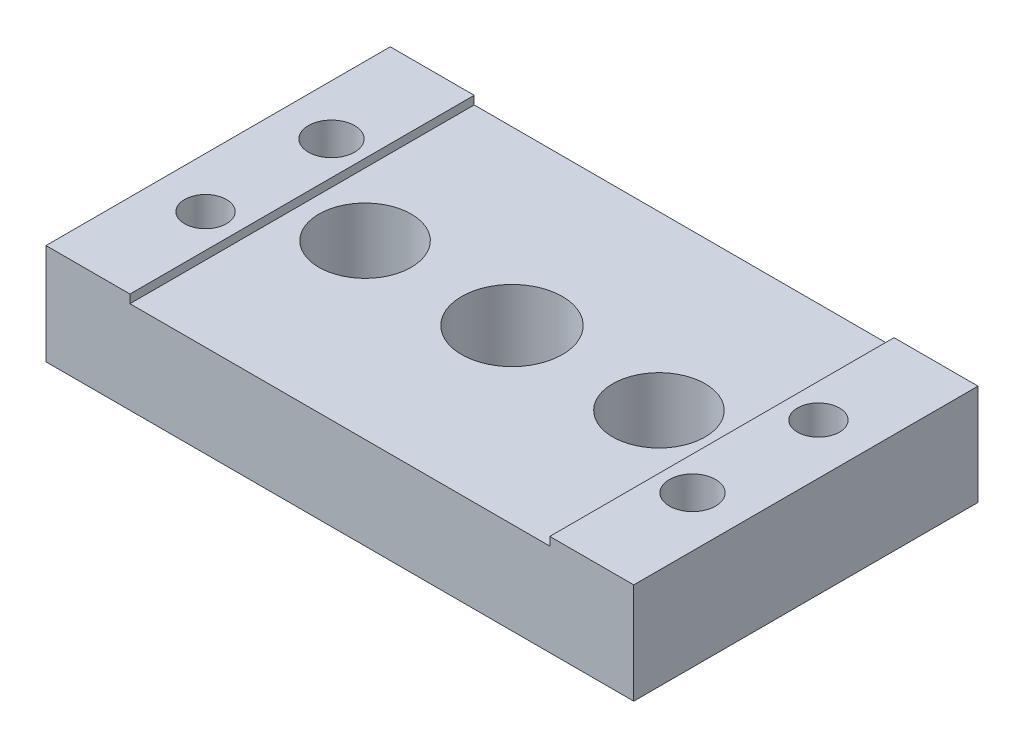
SolidWorks part; units mm, degrees
ref_plane "Front Plane" through (0, 0, 0) normal (0, 0, 1) x (1, 0, 0)
ref_plane "Top Plane" through (0, 0, 0) normal (0, 1, 0) x (1, 0, 0)
ref_plane "Right Plane" through (0, 0, 0) normal (1, 0, 0) x (0, 0, -1)
sketch "Sketch1" plane through (0, 0, 0) normal (0, 1, 0) x (1, 0, 0)
  line L1 (-35, 20.5) -> (35, 20.5)
  line L2 (-35, 20.5) -> (-35, -20.5)
  line L3 (-35, -20.5) -> (35, -20.5)
  line L4 (35, 20.5) -> (35, -20.5)
  line L5 (-35, 20.5) -> (35, -20.5) construction
  line L6 (-35, -20.5) -> (35, 20.5) construction
  point P0 (0, 0)
  dimension "D1" = 70
  dimension "D2" = 41
extrude "Boss-Extrude1" add sketch "Sketch1" along normal blind 12
sketch "Sketch2" plane through (0, 0, 20.5) normal (0, 0, 1) x (1, 0, 0)
  line L0 (-35, 12) -> (35, 12) construction
  line L1 (-25, 12) -> (25, 12)
  line L2 (-25, 12) -> (-25, 11)
  line L3 (-25, 11) -> (25, 11)
  line L4 (25, 12) -> (25, 11)
  line L5 (35, 12) -> (35, 0) construction
  line L6 (-35, 12) -> (-35, 0) construction
  dimension "D1" = 1
  dimension "D2" = 10
  dimension "D3" = 10
extrude "Cut-Extrude1" cut sketch "Sketch2" against normal blind 88
sketch "Sketch3" plane through (0, 0, 0) normal (0, -1, 0) x (1, 0, 0)
  line L0 (35, 20.5) -> (35, -20.5) construction
  line L1 (-35, -20.5) -> (-35, 20.5) construction
  line L2 (-35, 20.5) -> (35, 20.5) construction
  line L3 (35, -20.5) -> (-35, -20.5) construction
  circle A0 centre (29, -7.5) radius 2.5
  circle A1 centre (-29, 7.5) radius 2.5
  circle A2 centre (29, 7.5) radius 2.75
  circle A3 centre (-29, -7.5) radius 2.75
  dimension "D1" = 6
  dimension "D2" = 6
  dimension "D5" = 13
  dimension "D3" = 28
  dimension "D4" = 28
  dimension "D6" = 13
extrude "Cut-Extrude2" cut sketch "Sketch3" against normal blind 88
sketch "Sketch4" plane through (0, 0, 0) normal (0, -1, 0) x (1, 0, 0)
  circle A0 centre (-29, -7.5) radius 5
  circle A1 centre (29, 7.5) radius 5
extrude "Cut-Extrude3" cut sketch "Sketch4" against normal blind 5.7
sketch "Sketch5" plane through (0, 0, -20.5) normal (0, 0, -1) x (-1, 0, 0)
  line L0 (-35, 12) -> (-35, 0) construction
  circle A0 centre (-6.5, 6) radius 2.5
  dimension "D1" = 28.5
extrude "Cut-Extrude4" cut sketch "Sketch5" against normal blind 12
sketch "Sketch6" plane through (0, 0, 0) normal (0, -1, 0) x (1, 0, 0)
  line L0 (-35, -20.5) -> (-35, 20.5) construction
  line L1 (35, 20.5) -> (35, -20.5) construction
  circle A0 centre (0, 0) radius 6
  circle A1 centre (-17.5, 0) radius 5.5
  circle A2 centre (17.5, 0) radius 5.5
  point P11 (35, 0)
  dimension "D1" = 17.5
  dimension "D2" = 17.5
extrude "Cut-Extrude5" cut sketch "Sketch6" against normal blind 39
sketch "Sketch8" plane through (0, 0, -20.5) normal (0, 0, -1) x (-1, 0, 0)
  circle A0 centre (-6.5, 6) radius 2.5
extrude "Boss-Extrude2" add sketch "Sketch8" against normal up to surface (41 mm away) up to face at (0, 8.75, 20.5)
sketch "Sketch9" plane through (0, 0, -20.5) normal (0, 0, -1) x (-1, 0, 0)
  line L0 (-35, 0) -> (35, 0) construction
  line L1 (-35, 12) -> (-35, 0) construction
  circle A0 centre (-6.5, 5.5) radius 2.5
  dimension "D1" = 5.5
  dimension "D2" = 28.5
extrude "Cut-Extrude6" cut sketch "Sketch9" against normal blind 12
sketch "Sketch10" plane through (0, 11, 0) normal (0, 1, 0) x (1, 0, 0)
  circle A0 centre (0, 0) radius 6
extrude "Cut-Extrude7" cut sketch "Sketch10" against normal blind 30
